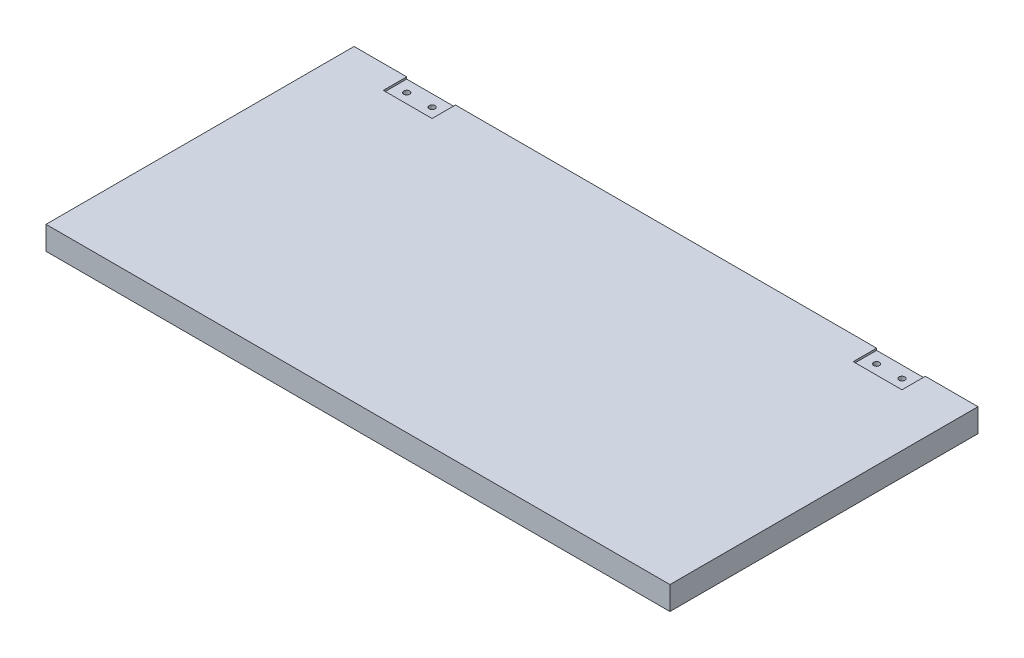
SolidWorks part; units mm, degrees
ref_plane "Front Plane" through (0, 0, 0) normal (0, 0, 1) x (1, 0, 0)
ref_plane "Top Plane" through (0, 0, 0) normal (0, 1, 0) x (1, 0, 0)
ref_plane "Right Plane" through (0, 0, 0) normal (1, 0, 0) x (0, 0, -1)
sketch "Sketch1" plane through (0, 0, 0) normal (0, 1, 0) x (1, 0, 0)
  line L1 (0, 0) -> (320, 0)
  line L2 (0, 0) -> (0, 158)
  line L3 (0, 158) -> (320, 158)
  line L4 (320, 0) -> (320, 158)
  dimension "D1" = 320
  dimension "D2" = 158
extrude "Boss-Extrude1" add sketch "Sketch1" along normal blind 12
sketch "Sketch2" plane through (0, 0, 0) normal (0, 1, 0) x (1, 0, 0)
  line L0 (320, 158) -> (0, 158) construction
  line L1 (27, 158) -> (52, 158)
  line L2 (27, 158) -> (27, 146)
  line L3 (27, 146) -> (52, 146)
  line L4 (52, 158) -> (52, 146)
  line L6 (268, 158) -> (293, 158)
  line L7 (268, 158) -> (268, 146)
  line L8 (268, 146) -> (293, 146)
  line L9 (293, 158) -> (293, 146)
  dimension "D1" = 27
  dimension "D2" = 25
  dimension "D3" = 12
  dimension "D4" = 27
  dimension "D5" = 25
  dimension "D6" = 12
extrude "Cut-Extrude1" cut sketch "Sketch2" against normal blind 1 from surface at 12 starting at face at (160, 12, -79)
sketch "Sketch3" plane through (0, 0, 0) normal (0, 1, 0) x (1, 0, 0)
  line L0 (0, 152) -> (320, 152) construction
  line L1 (0, 158) -> (0, 0) construction
  line L2 (320, 0) -> (320, 158) construction
  circle A0 centre (33, 152) radius 1.5
  circle A1 centre (46, 152) radius 1.5
  circle A2 centre (274, 152) radius 1.5
  circle A3 centre (287, 152) radius 1.5
  dimension "D2" = 3
  dimension "D3" = 3
  dimension "D6" = 3
  dimension "D7" = 3
  dimension "D8" = 13
  dimension "D1" = 6
  dimension "D4" = 33
  dimension "D5" = 13
  dimension "D9" = 33
extrude "Cut-Extrude5" cut sketch "Sketch3" along normal blind 9 from offset 3
